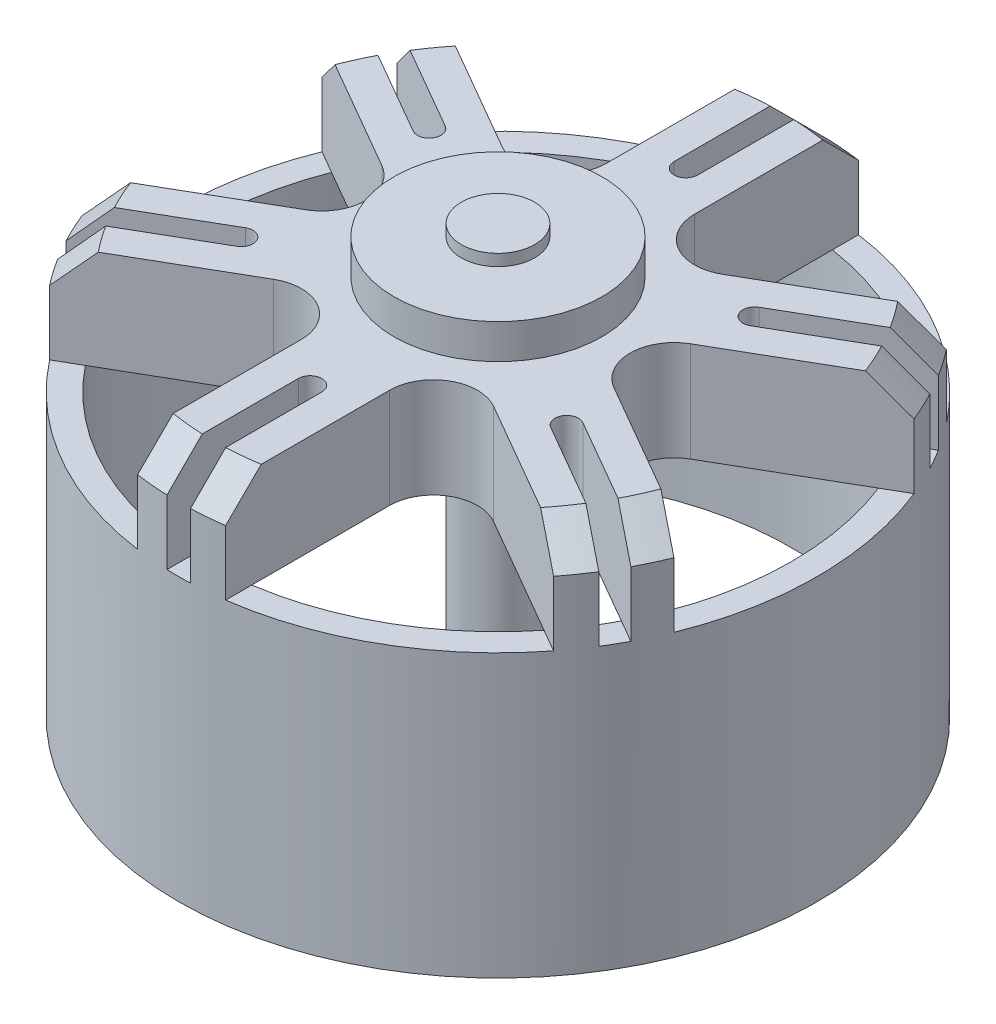
SolidWorks part; units mm, degrees
ref_plane "Front Plane" through (0, 0, 0) normal (0, 0, 1) x (1, 0, 0)
ref_plane "Top Plane" through (0, 0, 0) normal (0, 1, 0) x (1, 0, 0)
ref_plane "Right Plane" through (0, 0, 0) normal (1, 0, 0) x (0, 0, -1)
sketch "Sketch1" plane through (0, 0, 0) normal (0, 1, 0) x (1, 0, 0)
  circle A0 centre (0, 0) radius 13.8176
  circle A1 centre (0, 0) radius 12.7
  dimension "D1" = 27.6352
  dimension "D2" = 25.4
extrude "Boss-Extrude1" add sketch "Sketch1" along normal blind 16.5
sketch "Sketch2" plane through (0, 16.5, 0) normal (0, 1, 0) x (-1, 0, 0)
  circle A0 centre (0, 0) radius 13.8176
  circle A1 centre (0, 0) radius 13.8176 construction
extrude "Boss-Extrude2" add sketch "Sketch2" against normal blind 4.318
sketch "Sketch3" plane through (0, 16.5, 0) normal (0, 1, 0) x (-1, 0, 0)
  line L0 (-1.905, -13.6857) -> (-1.905, -6.5991)
  line L1 (-4.7625, -4.9493) -> (-10.8996, -8.4926)
  line L2 (0, 0) -> (0, -13.8176) construction
  line L3 (0, 0) -> (-11.9664, -6.9088) construction
  line L4 (-0.508, -13.8083) -> (-0.508, -8.128)
  line L5 (0, -7.62) -> (0, -13.8176)
  line L6 (-11.7043, -7.3441) -> (-6.7851, -4.5039)
  line L7 (-6.5991, -3.81) -> (-11.9664, -6.9088)
  line L8 (0, -7.62) -> (1.4425, -7.62) construction
  line L9 (-6.5991, -3.81) -> (-7.6722, -1.9514) construction
  circle A0 centre (0, 0) radius 13.8176 construction
  arc A1 (-1.905, -6.5991) -> (-4.7625, -4.9493) centre (-3.81, -6.5991) ccw
  arc A2 (-10.8996, -8.4926) -> (-1.905, -13.6857) centre (0, 0) ccw
  circle A3 centre (0, 0) radius 7.62 construction
  arc A4 (-0.508, -8.128) -> (0, -7.62) centre (0, -8.128) cw
  arc A5 (0, -13.8176) -> (-0.508, -13.8083) centre (0, 0) cw
  arc A6 (-6.7851, -4.5039) -> (-6.5991, -3.81) centre (-7.0391, -4.064) ccw
  arc A7 (-11.9664, -6.9088) -> (-11.7043, -7.3441) centre (0, 0) ccw
  point P24 (0, -7.62)
  point P25 (-6.5991, -3.81)
  dimension "D1" = 15.24
  dimension "D2" = 60
  dimension "D3" = 3.81
  dimension "D4" = 3.81
  dimension "D5" = 0.508
  dimension "D6" = 0.508
extrude "Cut-Extrude1" cut sketch "Sketch3" against normal up to surface (4.318 mm away) up to face at (0, 12.182, 12.7)
pattern_circular "CirPattern1" count 6 over 360 about axis through (0, 0, 0) along (0, 1, 0) of "Cut-Extrude1"
chamfer "Chamfer1" distance 1.524 angle 45 12 edges at (-1.2081, 16.5, 13.7647) (-11.3165, 16.5, 7.9286) (-12.5246, 16.5, 5.8361) (-12.5246, 16.5, -5.8361) (-11.3165, 16.5, -7.9286) (-1.2081, 16.5, -13.7647) (1.2081, 16.5, -13.7647) (11.3165, 16.5, -7.9286) (12.5246, 16.5, -5.8361) (12.5246, 16.5, 5.8361) (11.3165, 16.5, 7.9286) (1.2081, 16.5, 13.7647)
sketch "Sketch4" plane through (0, 16.5, 0) normal (0, 1, 0) x (-1, 0, 0)
  circle A0 centre (0, 0) radius 4.5
  dimension "D1" = 9
extrude "Boss-Extrude3" add sketch "Sketch4" along normal blind 1.5
sketch "Sketch5" plane through (0, 18, 0) normal (0, 1, 0) x (-1, 0, 0)
  circle A0 centre (0, 0) radius 1.5875
  dimension "D1" = 3.175
extrude "Boss-Extrude4" add sketch "Sketch5" against normal blind 26 and the other way blind 0.5
